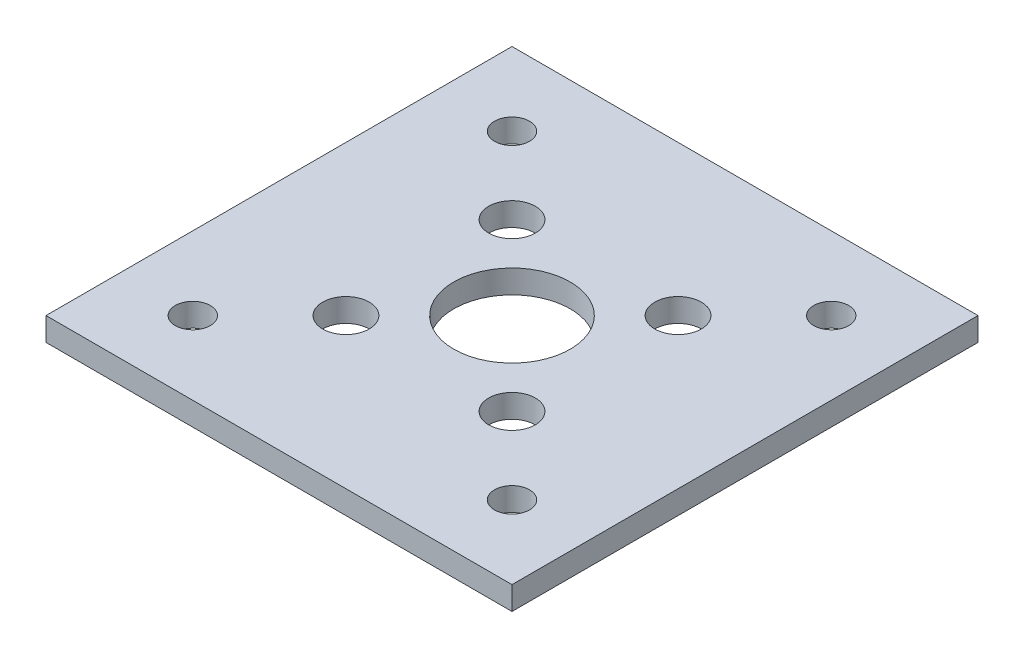
SolidWorks part; units mm, degrees
ref_plane "Front Plane" through (0, 0, 0) normal (0, 0, 1) x (1, 0, 0)
ref_plane "Top Plane" through (0, 0, 0) normal (0, 1, 0) x (1, 0, 0)
ref_plane "Right Plane" through (0, 0, 0) normal (1, 0, 0) x (0, 0, -1)
sketch "Sketch1" plane through (0, 0, 0) normal (0, 1, 0) x (1, 0, 0)
  line L1 (-31.75, -31.75) -> (31.75, -31.75)
  line L2 (-31.75, -31.75) -> (-31.75, 31.75)
  line L3 (-31.75, 31.75) -> (31.75, 31.75)
  line L4 (31.75, -31.75) -> (31.75, 31.75)
  line L5 (-31.75, -31.75) -> (31.75, 31.75) construction
  line L6 (-31.75, 31.75) -> (31.75, -31.75) construction
  point P0 (0, 0)
  dimension "D1" = 63.5
  dimension "D2" = 63.5
extrude "Boss-Extrude1" add sketch "Sketch1" along normal blind 3.175
sketch "Sketch2" plane through (0, 3.175, 0) normal (0, 1, 0) x (1, 0, 0)
  line L0 (0, 0) -> (11.3137, 11.3137) construction
  line L1 (0, 0) -> (0, 7.779) construction
  line L2 (-31.75, 31.75) -> (-31.75, -31.75) construction
  line L3 (-21.75, -21.75) -> (21.75, -21.75) construction
  line L4 (-21.75, -21.75) -> (-21.75, 21.75) construction
  line L5 (-21.75, 21.75) -> (21.75, 21.75) construction
  line L6 (21.75, -21.75) -> (21.75, 21.75) construction
  line L7 (-21.75, -21.75) -> (21.75, 21.75) construction
  line L8 (-21.75, 21.75) -> (21.75, -21.75) construction
  line L9 (-31.75, -31.75) -> (31.75, -31.75) construction
  circle A0 centre (0, 0) radius 16 construction
  circle A1 centre (11.3137, 11.3137) radius 3.175
  circle A2 centre (11.3137, -11.3137) radius 3.175
  circle A3 centre (-11.3137, -11.3137) radius 3.175
  circle A4 centre (-11.3137, 11.3137) radius 3.175
  circle A5 centre (0, 0) radius 7.9375
  circle A6 centre (-21.75, -21.75) radius 2.3812
  circle A7 centre (21.75, -21.75) radius 2.3812
  circle A8 centre (21.75, 21.75) radius 2.3812
  circle A9 centre (-21.75, 21.75) radius 2.3812
  point P15 (0, 0)
  dimension "D1" = 6.35
  dimension "D2" = 32
  dimension "D5" = 15.875
  dimension "D8" = 4.7625
  dimension "D3" = 45
  dimension "D6" = 10
  dimension "D7" = 10
  dimension "D4" = 4
extrude "Cut-Extrude1" cut sketch "Sketch2" against normal through all contours A5
